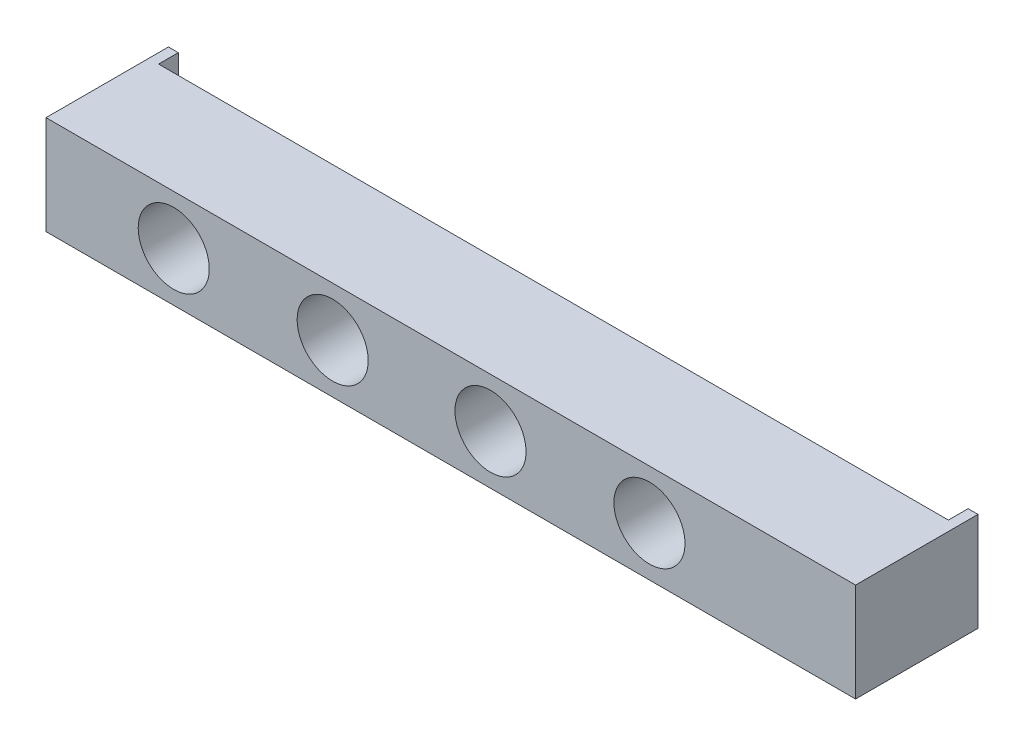
SolidWorks part; units mm, degrees
ref_plane "Ebene vorne" through (0, 0, 0) normal (0, 0, 1) x (1, 0, 0)
ref_plane "Ebene oben" through (0, 0, 0) normal (0, 1, 0) x (1, 0, 0)
ref_plane "Ebene rechts" through (0, 0, 0) normal (1, 0, 0) x (0, 0, -1)
sketch "Skizze1" plane through (0, 0, 0) normal (0, 0, 1) x (1, 0, 0)
  line L1 (0, 0) -> (205, 0)
  line L2 (0, 0) -> (0, 25)
  line L3 (0, 25) -> (205, 25)
  line L4 (205, 0) -> (205, 25)
  dimension "D1" = 205
  dimension "D2" = 25
extrude "Aufsatz-Linear austragen1" add sketch "Skizze1" along normal blind 26
sketch "Skizze2" plane through (0, 0, 0) normal (0, 0, -1) x (-1, 0, 0)
  line L0 (0, 0) -> (-205, 0) construction
  line L1 (0, 25) -> (-2.5, 25)
  line L2 (0, 25) -> (0, 0)
  line L3 (0, 0) -> (-2.5, 0)
  line L4 (-2.5, 25) -> (-2.5, 0)
  line L6 (-205, 25) -> (-202.5, 25)
  line L7 (-205, 25) -> (-205, 0)
  line L8 (-205, 0) -> (-202.5, 0)
  line L9 (-202.5, 25) -> (-202.5, 0)
  dimension "D1" = 2.5
  dimension "D2" = 2.5
extrude "Aufsatz-Linear austragen2" add sketch "Skizze2" along normal blind 5
hole_wizard "Ø18.0 (18) Durchmesser Bohrung1" positions "Skizze13" profile "Skizze14" hole size "Ø18.0" standard "DIN" end condition through all
sketch "Skizze13" plane through (0, 0, 0) normal (0, 0, -1) x (-1, 0, 0)
  point P0 (-32.3443, 12.5)
  point P2 (-72.5887, 12.5)
  point P4 (-112.5611, 12.5)
  point P6 (-152.8054, 12.5)
sketch "Skizze14" plane through (32.3443, 12.5, 0) normal (1, 0, 0) x (0, 1, 0)
  line L0 (0, 0) -> (0, 26)
  line L1 (0, 26) -> (9, 26)
  line L2 (9, 26) -> (9, 0)
  line L5 (9, 0) -> (0, 0)
  line L11 (0, -6.35) -> (0, 107.95) construction
  dimension "Bohrerdurchmesser" = 18
  dimension "Bohrungstiefe" = 26
